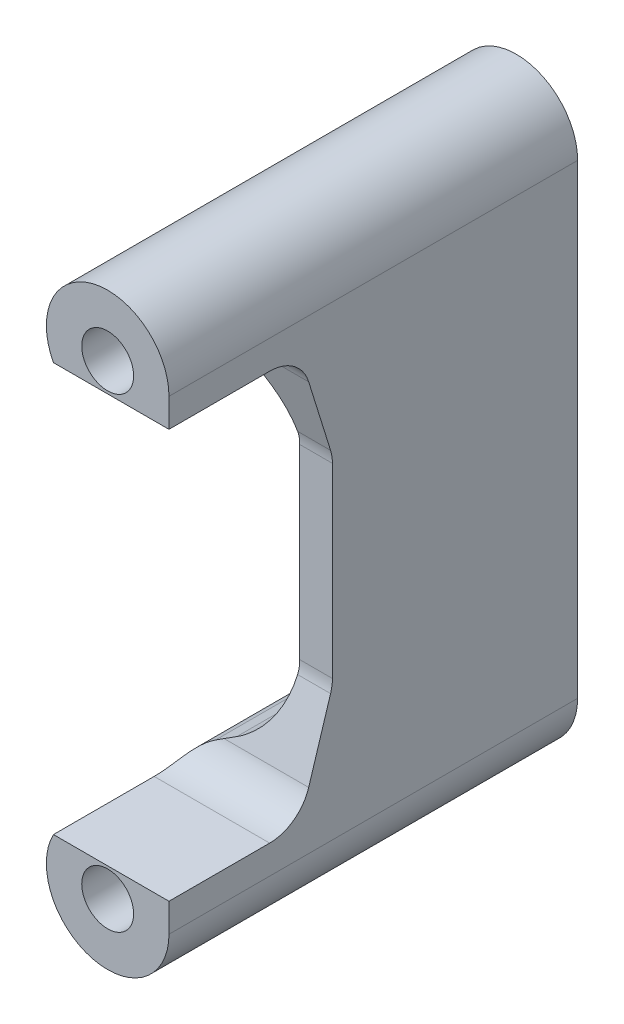
SolidWorks part; units mm, degrees
material "ABS"
ref_plane "Alzado" through (0, 0, 0) normal (0, 0, 1) x (1, 0, 0)
ref_plane "Planta" through (0, 0, 0) normal (0, 1, 0) x (1, 0, 0)
ref_plane "Vista lateral" through (0, 0, 0) normal (1, 0, 0) x (0, 0, -1)
sketch "Croquis1" plane through (0, 0, 0) normal (0, 0, 1) x (1, 0, 0)
  line L5 (-13.465, 0) -> (13.8234, 0) construction
  line L8 (-4, 17.8433) -> (-11.2336, 21.9954)
  line L9 (-4, 17.8433) -> (-4, -17.8433)
  line L10 (0, 28.5) -> (0, -28.5)
  line L11 (-4, -17.8433) -> (-11.2336, -21.9954)
  circle A0 centre (-7.5, 28.5) radius 3.175
  arc A5 (0, 28.5) -> (-11.2336, 21.9954) centre (-7.5, 28.5) ccw
  arc A6 (0, -28.5) -> (-11.2336, -21.9954) centre (-7.5, -28.5) cw
  circle A7 centre (-7.5, -28.5) radius 3.175
  point P7 (0, 0)
  point P15 (0, 0)
  point P16 (-4, 0)
  point P17 (-4, 0)
  dimension "D1" = 6.35
  dimension "D2" = 57
  dimension "D3" = 4
  dimension "D4" = 7.5
extrude "Saliente-Extruir1" add sketch "Croquis1" along normal mid plane 50
fillet "Redondeo1" radius 10 2 edges at (-4, -17.8433, 0) (-4, 17.8433, 0)
sketch "Croquis2" plane through (0, 0, 0) normal (1, 0, 0) x (0, 0, -1)
  line L0 (-9, 25) -> (-5, 12.1593)
  line L1 (-5, 12.1593) -> (-5, -12.1593)
  line L2 (-29.8735, 0) -> (35.3957, 0) construction
  line L3 (-9, 25) -> (-29.8735, 25)
  line L4 (-29.8735, 25) -> (-29.8735, -25)
  line L5 (-9, -25) -> (-29.8735, -25)
  line L6 (-9, -25) -> (-5, -12.1593)
  line L7 (-25, -28.5) -> (-25, 28.5) construction
  point P10 (-5, 0)
  dimension "D1" = 50
  dimension "D2" = 20
  dimension "D3" = 16
extrude "Cortar-Extruir1" cut sketch "Croquis2" against normal through all
fillet "Redondeo2" radius 5 4 edges at (-2.0003, 12.1593, 5) (-2.0003, -12.1593, 5) (-7.0666, -25, 9) (-7.0666, 25, 9)
